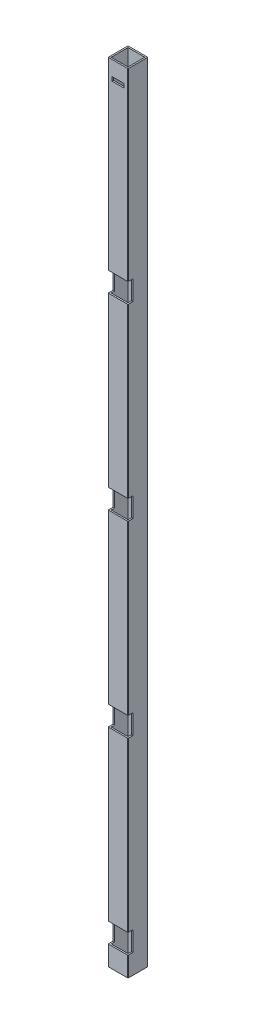
SolidWorks part; units mm, degrees
ref_plane "Front Plane" through (0, 0, 0) normal (0, 0, 1) x (1, 0, 0)
ref_plane "Top Plane" through (0, 0, 0) normal (0, 1, 0) x (1, 0, 0)
ref_plane "Right Plane" through (0, 0, 0) normal (1, 0, 0) x (0, 0, -1)
sketch "Sketch1" plane through (0, 0, 0) normal (0, 1, 0) x (1, 0, 0)
  line L0 (1.5, 1.5) -> (18.5, 1.5)
  line L1 (0.5, 0) -> (19.5, 0)
  line L2 (0, 0.5) -> (0, 19.5)
  line L3 (0.5, 20) -> (19.5, 20)
  line L4 (20, 0.5) -> (20, 19.5)
  line L5 (18.5, 1.5) -> (18.5, 18.5)
  line L6 (1.5, 18.5) -> (18.5, 18.5)
  line L7 (1.5, 1.5) -> (1.5, 18.5)
  arc A0 (19.5, 0) -> (20, 0.5) centre (19.5, 0.5) ccw
  arc A1 (0.5, 0) -> (0, 0.5) centre (0.5, 0.5) cw
  arc A2 (0, 19.5) -> (0.5, 20) centre (0.5, 19.5) cw
  arc A3 (19.5, 20) -> (20, 19.5) centre (19.5, 19.5) cw
  arc A4 (18.5, 1.5) -> (18.5, 1.5) centre (18.5, 1.5) ccw
  arc A5 (18.5, 18.5) -> (18.5, 18.5) centre (18.5, 18.5) cw
  arc A6 (1.5, 18.5) -> (1.5, 18.5) centre (1.5, 18.5) cw
  arc A7 (1.5, 1.5) -> (1.5, 1.5) centre (1.5, 1.5) cw
  point P9 (0, 0)
  dimension "D3" = 0.5
  dimension "D1" = 20
  dimension "D2" = 20
  dimension "D4" = 1.5
extrude "Boss-Extrude1" add sketch "Sketch1" along normal blind 796.5
sketch "Sketch3" plane through (0, 0, 0) normal (0, 0, 1) x (1, 0, 0)
  line L0 (0.5, 796.5) -> (19.5, 796.5) construction
  line L1 (16, 781.5) -> (4, 781.5)
  line L2 (16, 781.5) -> (16, 777.5)
  line L3 (16, 777.5) -> (4, 777.5)
  line L4 (4, 781.5) -> (4, 777.5)
  line L5 (10, 781.5) -> (10, 796.5) construction
  dimension "D1" = 4
  dimension "D2" = 12
  dimension "D3" = 15
extrude "Cut-Extrude1" cut sketch "Sketch3" against normal blind 10
sketch "Sketch5" plane through (0, 0, 0) normal (-1, 0, 0) x (0, 0, 1)
  line L0 (0, 796.5) -> (0, 0) construction
  line L1 (0, 610) -> (-5, 610)
  line L2 (0, 610) -> (0, 590)
  line L3 (0, 590) -> (-5, 590)
  line L4 (-5, 610) -> (-5, 590)
  line L5 (-19.5, 796.5) -> (-0.5, 796.5) construction
  line L6 (0, 420) -> (-5, 420)
  line L7 (0, 420) -> (0, 400)
  line L8 (0, 400) -> (-5, 400)
  line L9 (-5, 420) -> (-5, 400)
  line L10 (0, 230) -> (-5, 230)
  line L11 (0, 230) -> (0, 210)
  line L12 (0, 210) -> (-5, 210)
  line L13 (-5, 230) -> (-5, 210)
  line L14 (0, 40) -> (-5, 40)
  line L15 (0, 40) -> (0, 20)
  line L16 (0, 20) -> (-5, 20)
  line L17 (-5, 40) -> (-5, 20)
  dimension "D1" = 186.5
  dimension "D2" = 20
  dimension "D3" = 5
  dimension "D4" = 4
extrude "Cut-Extrude2" cut sketch "Sketch5" against normal through all
